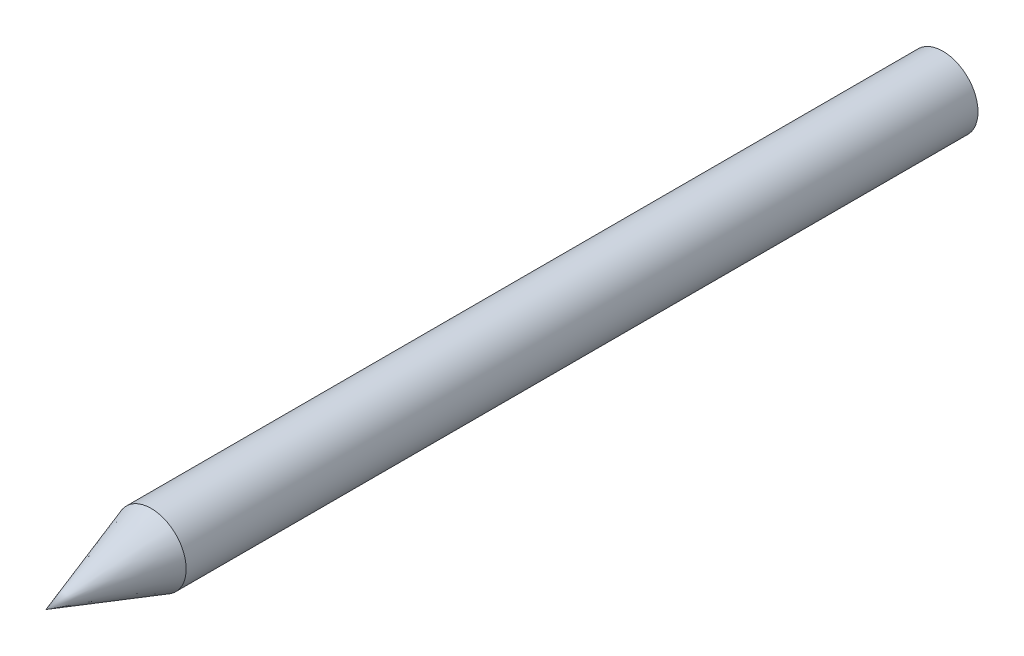
SolidWorks part; units mm, degrees
ref_plane "Plan de face" through (0, 0, 0) normal (0, 0, 1) x (1, 0, 0)
ref_plane "Plan de dessus" through (0, 0, 0) normal (0, 1, 0) x (1, 0, 0)
ref_plane "Plan de droite" through (0, 0, 0) normal (1, 0, 0) x (0, 0, -1)
sketch "Esquisse1" plane through (0, 0, 0) normal (0, 0, 1) x (1, 0, 0)
  circle A0 centre (0, 0) radius 5
extrude "Boss.-Extru.1" add sketch "Esquisse1" along normal blind 128
chamfer "Chanfrein1" distance 15 distance2 5 1 edges at (5, 0, 128)
